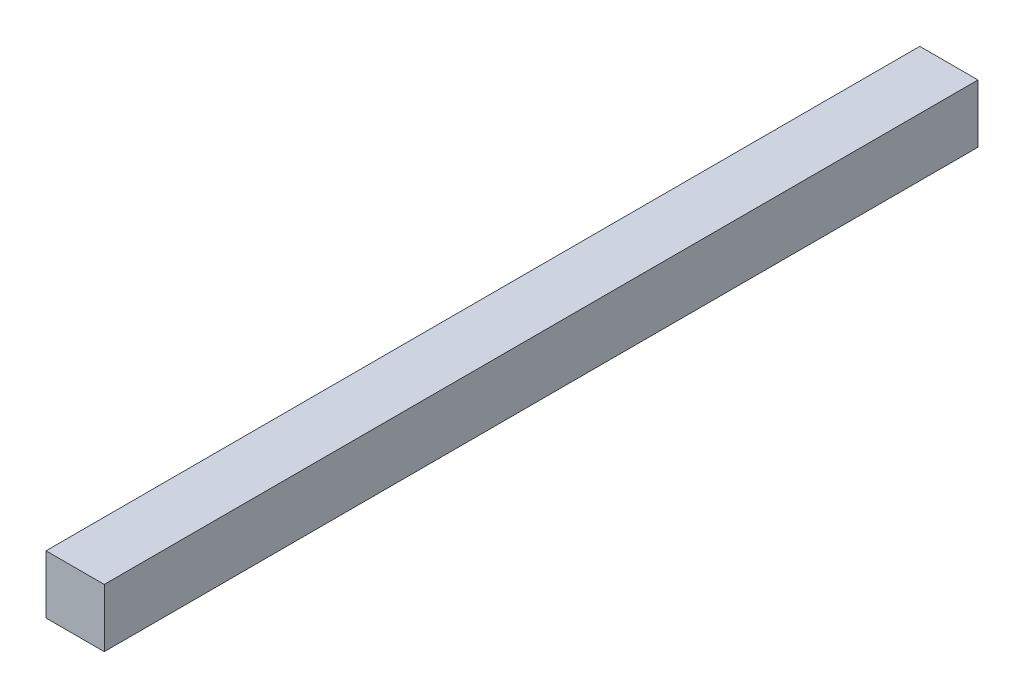
SolidWorks part; units mm, degrees
ref_plane "Front Plane" through (0, 0, 0) normal (0, 0, 1) x (1, 0, 0)
ref_plane "Top Plane" through (0, 0, 0) normal (0, 1, 0) x (1, 0, 0)
ref_plane "Right Plane" through (0, 0, 0) normal (1, 0, 0) x (0, 0, -1)
sketch "Sketch7" plane through (0, 0, 0) normal (0, 0, 1) x (1, 0, 0)
  line L1 (-10.16, -10.16) -> (10.16, -10.16)
  line L2 (-10.16, -10.16) -> (-10.16, 10.16)
  line L3 (-10.16, 10.16) -> (10.16, 10.16)
  line L4 (10.16, -10.16) -> (10.16, 10.16)
  line L5 (-10.16, -10.16) -> (10.16, 10.16) construction
  line L6 (-10.16, 10.16) -> (10.16, -10.16) construction
  point P0 (0, 0)
  dimension "D1" = 20.32
extrude "Boss-Extrude3" add sketch "Sketch7" along normal mid plane 304.8
